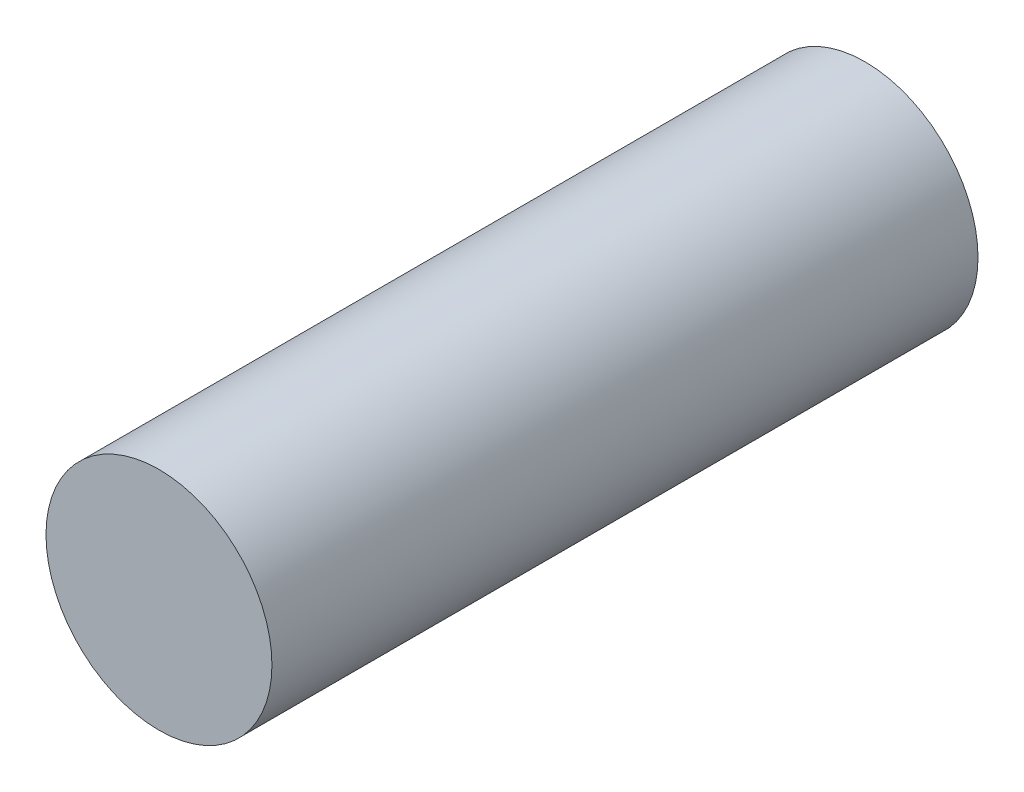
SolidWorks part; units mm, degrees
ref_plane "Front Plane" through (0, 0, 0) normal (0, 0, 1) x (1, 0, 0)
ref_plane "Top Plane" through (0, 0, 0) normal (0, 1, 0) x (1, 0, 0)
ref_plane "Right Plane" through (0, 0, 0) normal (1, 0, 0) x (0, 0, -1)
sketch "Sketch2" plane through (0, 0, 0) normal (0, 0, 1) x (1, 0, 0)
  circle A0 centre (0, 0) radius 8
  dimension "D1" = 16
extrude "Boss-Extrude1" add sketch "Sketch2" along normal blind 50
